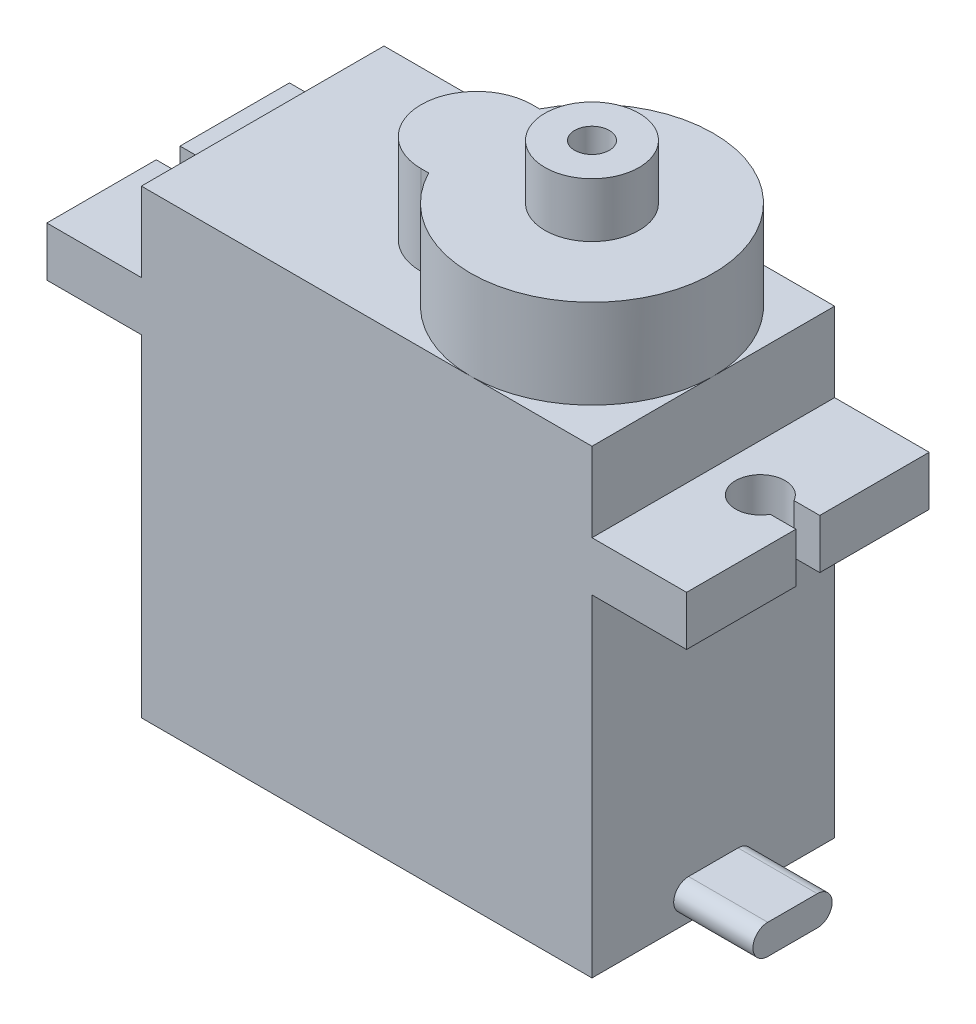
SolidWorks part; units mm, degrees
material "Nylon 101"
ref_plane "Front plane" through (0, 0, 0) normal (0, 0, 1) x (1, 0, 0)
ref_plane "Top plane" through (0, 0, 0) normal (0, 1, 0) x (1, 0, 0)
ref_plane "Right Plane" through (0, 0, 0) normal (1, 0, 0) x (0, 0, -1)
sketch "Sketch1" plane through (0, 0, 0) normal (0, 1, 0) x (1, 0, 0)
  line L1 (-11.375, -6.125) -> (11.375, -6.125)
  line L2 (-11.375, -6.125) -> (-11.375, 6.125)
  line L3 (-11.375, 6.125) -> (11.375, 6.125)
  line L4 (11.375, -6.125) -> (11.375, 6.125)
  line L5 (-11.375, -6.125) -> (11.375, 6.125) construction
  line L6 (-11.375, 6.125) -> (11.375, -6.125) construction
  point P0 (0, 0)
  dimension "D1" = 22.75
  dimension "D2" = 12.25
extrude "Boss-Extrude1" add sketch "Sketch1" along normal blind 16.75
sketch "Sketch3" plane through (0, 16.75, 0) normal (0, 1, 0) x (1, 0, 0)
  line L0 (11.375, 6.125) -> (-11.375, 6.125) construction
  line L1 (-16.15, -6.125) -> (16.15, -6.125)
  line L2 (-16.15, -6.125) -> (-16.15, -0.6)
  line L3 (-16.15, 6.125) -> (16.15, 6.125)
  line L4 (16.15, -6.125) -> (16.15, -0.6)
  line L5 (-16.15, -6.125) -> (16.15, 6.125) construction
  line L6 (-16.15, 6.125) -> (16.15, -6.125) construction
  line L7 (16.15, 0.6) -> (16.15, 6.125)
  line L8 (14.8466, 0.6) -> (16.15, 0.6)
  line L10 (14.8466, -0.6) -> (16.15, -0.6)
  line L12 (0, 0) -> (0, 6.125) construction
  line L13 (-14.8466, -0.6) -> (-16.15, -0.6)
  line L14 (-14.8466, 0.6) -> (-16.15, 0.6)
  line L15 (-16.15, 0.6) -> (-16.15, 6.125)
  arc A0 (14.8466, 0.6) -> (14.8466, -0.6) centre (13.75, 0) ccw
  arc A1 (-14.8466, 0.6) -> (-14.8466, -0.6) centre (-13.75, 0) cw
  point P0 (0, 0)
  dimension "D3" = 1.25
  dimension "D1" = 32.3
  dimension "D2" = 1.2
  dimension "D4" = 27.5
extrude "Boss-Extrude2" add sketch "Sketch3" along normal blind 2.5
sketch "Sketch4" plane through (0, 16.75, 0) normal (0, -1, 0) x (1, 0, 0)
  line L72 (-11.375, -5.125) -> (-15.15, -5.125)
  line L73 (-15.15, -5.125) -> (-15.15, -1.7614)
  line L74 (-15.15, 1.7614) -> (-15.15, 5.125)
  line L75 (-15.15, 5.125) -> (-11.375, 5.125)
  line L76 (-11.375, -5.125) -> (-15.15, -5.125)
  line L77 (-15.15, -5.125) -> (-15.15, -1.7614)
  line L78 (-15.15, 1.7614) -> (-15.15, 5.125)
  line L79 (-15.15, 5.125) -> (-11.375, 5.125)
  line L181 (-11.375, -6.125) -> (-11.375, 6.125) construction
  line L182 (11.375, 6.125) -> (11.375, -6.125) construction
  line L183 (-11.375, -5.125) -> (-11.375, 5.125)
  line L184 (11.375, 5.125) -> (11.375, -5.125)
  line L187 (15.15, -5.125) -> (11.375, -5.125)
  line L188 (15.15, -1.7614) -> (15.15, -5.125)
  line L189 (15.15, 5.125) -> (15.15, 1.7614)
  line L190 (11.375, 5.125) -> (15.15, 5.125)
  line L191 (15.15, -5.125) -> (11.375, -5.125)
  line L192 (15.15, -1.7614) -> (15.15, -5.125)
  line L193 (15.15, 5.125) -> (15.15, 1.7614)
  line L194 (11.375, 5.125) -> (15.15, 5.125)
  arc A11 (-15.15, -1.7614) -> (-15.15, 1.7614) centre (-13.75, 0) ccw
  arc A12 (-15.15, -1.7614) -> (-15.15, 1.7614) centre (-13.75, 0) ccw
  arc A33 (15.15, 1.7614) -> (15.15, -1.7614) centre (13.75, 0) ccw
  arc A34 (15.15, 1.7614) -> (15.15, -1.7614) centre (13.75, 0) ccw
  dimension "D1" = 1
  dimension "D2" = 1
extrude "Cut-Extrude1" cut sketch "Sketch4" against normal blind 1
sketch "Sketch5" plane through (0, 19.25, 0) normal (0, 1, 0) x (1, 0, 0)
  line L0 (16.15, 6.125) -> (-16.15, 6.125) construction
  line L1 (-11.375, -6.125) -> (11.375, -6.125)
  line L2 (-11.375, -6.125) -> (-11.375, 6.125)
  line L3 (-11.375, 6.125) -> (11.375, 6.125)
  line L4 (11.375, -6.125) -> (11.375, 6.125)
  line L5 (-11.375, -6.125) -> (11.375, 6.125) construction
  line L6 (-11.375, 6.125) -> (11.375, -6.125) construction
  point P0 (0, 0)
  dimension "D1" = 22.75
extrude "Boss-Extrude3" add sketch "Sketch5" along normal blind 4
sketch "Sketch6" plane through (0, 23.25, 0) normal (0, 1, 0) x (1, 0, 0)
  line L0 (11.375, -6.125) -> (11.375, 6.125) construction
  line L1 (-0.575, 2.8) -> (-0.1975, 2.8)
  line L2 (-0.575, -2.8) -> (-0.1975, -2.8)
  line L3 (11.375, 6.125) -> (-11.375, 6.125) construction
  line L4 (11.375, -6.125) -> (11.375, 6.125) construction
  arc A0 (-0.1975, -2.8) -> (-0.1975, 2.8) centre (5.25, 0) ccw
  arc A1 (-0.575, 2.8) -> (-0.575, -2.8) centre (-0.575, 0) ccw
  point P12 (-3.375, 0)
  dimension "D1" = 5.6
  dimension "D2" = 14.75
extrude "Boss-Extrude4" add sketch "Sketch6" along normal blind 4.5
sketch "Sketch7" plane through (0, 27.75, 0) normal (0, 1, 0) x (1, 0, 0)
  circle A0 centre (5.25, 0) radius 2.375
  circle A1 centre (5.25, 0) radius 0.875
  dimension "D1" = 4.75
  dimension "D2" = 1.75
extrude "Boss-Extrude5" add sketch "Sketch7" along normal blind 2.75
sketch "Sketch8" plane through (11.375, 0, 0) normal (1, 0, 0) x (0, 0, -1)
  line L0 (-1.25, 1.25) -> (1.25, 1.25) construction
  line L1 (-1.25, 2) -> (1.25, 2)
  line L2 (-1.25, 0.5) -> (1.25, 0.5)
  line L3 (-6.125, 0) -> (6.125, 0) construction
  arc A0 (-1.25, 2) -> (-1.25, 0.5) centre (-1.25, 1.25) ccw
  arc A1 (1.25, 0.5) -> (1.25, 2) centre (1.25, 1.25) ccw
  point P2 (0, 1.25)
  point P7 (2, 1.25)
  point P8 (-2, 1.25)
  point P13 (0, 0)
  dimension "D1" = 1.5
  dimension "D2" = 4
  dimension "D3" = 0.5
extrude "Boss-Extrude6" add sketch "Sketch8" along normal blind 4
